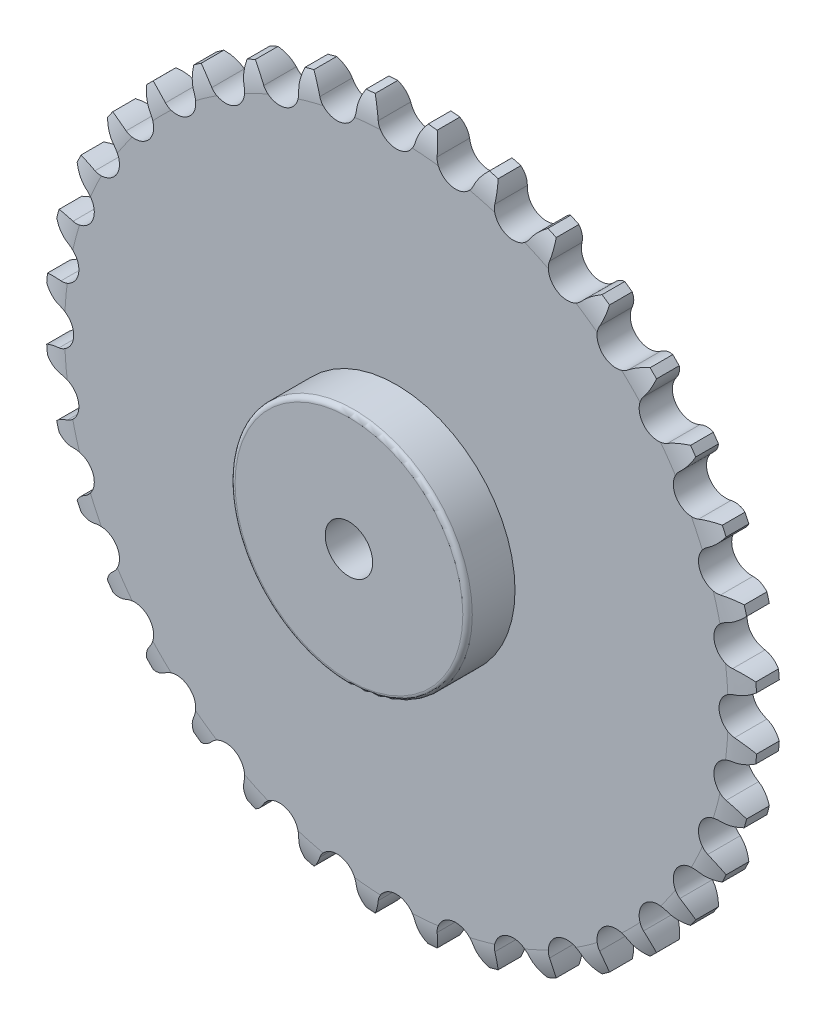
SolidWorks part; units mm, degrees
ref_plane "Front Plane" through (0, 0, 0) normal (0, 0, 1) x (1, 0, 0)
ref_plane "Top Plane" through (0, 0, 0) normal (0, 1, 0) x (1, 0, 0)
ref_plane "Right Plane" through (0, 0, 0) normal (1, 0, 0) x (0, 0, -1)
sketch "Sketch1" plane through (0, 0, 0) normal (0, 0, 1) x (1, 0, 0)
  line L0 (0, 0) -> (0, 75) construction
  line L1 (0, 0) -> (13.6677, 73.7441) construction
  circle A0 centre (0, 0) radius 15
  arc A1 (32.5641, 67.5617) -> (30.8234, 68.3734) centre (0, 0) ccw
  circle A2 centre (0, 0) radius 70.5 construction
  circle A3 centre (0, 0) radius 72 construction
  arc A4 (-3.9118, 71.1646) -> (3.9118, 71.1646) centre (0, 72) ccw
  arc A6 (5.5795, 74.7922) -> (3.9118, 71.1646) centre (12.8364, 69.2588) ccw
  arc A7 (-5.5795, 74.7922) -> (-3.9118, 71.1646) centre (-12.8364, 69.2588) cw
  arc A8 (7.4928, 74.6248) -> (8.5052, 70.7628) centre (-0.6147, 70.4356) cw
  arc A9 (18.4823, 72.687) -> (16.21, 69.4042) centre (24.668, 65.9776) ccw
  arc A10 (8.5052, 70.7628) -> (16.21, 69.4042) centre (12.5027, 70.9062) ccw
  arc A11 (20.3374, 72.19) -> (20.6639, 68.2108) centre (11.6257, 69.4723) cw
  arc A12 (30.8234, 68.3734) -> (28.0156, 65.535) centre (35.7502, 60.6917) ccw
  arc A13 (20.6639, 68.2108) -> (28.0156, 65.535) centre (24.6255, 67.6579) ccw
  arc A14 (32.5641, 67.5617) -> (32.1946, 63.5863) centre (23.5128, 66.3981) cw
  arc A15 (42.2281, 61.9822) -> (38.97, 59.6745) centre (45.746, 53.5617) ccw
  arc A16 (32.1946, 63.5863) -> (38.97, 59.6745) centre (36, 62.3538) ccw
  arc A17 (43.8013, 60.8806) -> (42.7471, 57.0297) centre (34.6855, 61.3064) cw
  arc A18 (52.3496, 53.7077) -> (48.7404, 52.0008) centre (54.3519, 44.8043) ccw
  arc A19 (42.7471, 57.0297) -> (48.7404, 52.0008) centre (46.2807, 55.1552) ccw
  arc A20 (53.7077, 52.3496) -> (52.0008, 48.7404) centre (44.8043, 54.3519) cw
  arc A21 (60.8806, 43.8013) -> (57.0297, 42.7471) centre (61.3064, 34.6855) ccw
  arc A22 (52.0008, 48.7404) -> (57.0297, 42.7471) centre (55.1552, 46.2807) ccw
  arc A23 (61.9822, 42.2281) -> (59.6745, 38.97) centre (53.5617, 45.746) cw
  arc A24 (67.5617, 32.5641) -> (63.5863, 32.1946) centre (66.3981, 23.5128) ccw
  arc A25 (59.6745, 38.97) -> (63.5863, 32.1946) centre (62.3538, 36) ccw
  arc A26 (68.3734, 30.8234) -> (65.535, 28.0156) centre (60.6917, 35.7502) cw
  arc A27 (72.19, 20.3374) -> (68.2108, 20.6639) centre (69.4723, 11.6257) ccw
  arc A28 (65.535, 28.0156) -> (68.2108, 20.6639) centre (67.6579, 24.6255) ccw
  arc A29 (72.687, 18.4823) -> (69.4042, 16.21) centre (65.9776, 24.668) cw
  arc A30 (74.6248, 7.4928) -> (70.7628, 8.5052) centre (70.4356, -0.6147) ccw
  arc A31 (69.4042, 16.21) -> (70.7628, 8.5052) centre (70.9062, 12.5027) ccw
  arc A32 (74.7922, 5.5795) -> (71.1646, 3.9118) centre (69.2588, 12.8364) cw
  arc A33 (74.7922, -5.5795) -> (71.1646, -3.9118) centre (69.2588, -12.8364) ccw
  arc A34 (71.1646, 3.9118) -> (71.1646, -3.9118) centre (72, 0) ccw
  arc A35 (74.6248, -7.4928) -> (70.7628, -8.5052) centre (70.4356, 0.6147) cw
  arc A36 (72.687, -18.4823) -> (69.4042, -16.21) centre (65.9776, -24.668) ccw
  arc A37 (70.7628, -8.5052) -> (69.4042, -16.21) centre (70.9062, -12.5027) ccw
  arc A38 (72.19, -20.3374) -> (68.2108, -20.6639) centre (69.4723, -11.6257) cw
  arc A39 (68.3734, -30.8234) -> (65.535, -28.0156) centre (60.6917, -35.7502) ccw
  arc A40 (68.2108, -20.6639) -> (65.535, -28.0156) centre (67.6579, -24.6255) ccw
  arc A41 (67.5617, -32.5641) -> (63.5863, -32.1946) centre (66.3981, -23.5128) cw
  arc A42 (61.9822, -42.2281) -> (59.6745, -38.97) centre (53.5617, -45.746) ccw
  arc A43 (63.5863, -32.1946) -> (59.6745, -38.97) centre (62.3538, -36) ccw
  arc A44 (60.8806, -43.8013) -> (57.0297, -42.7471) centre (61.3064, -34.6855) cw
  arc A45 (53.7077, -52.3496) -> (52.0008, -48.7404) centre (44.8043, -54.3519) ccw
  arc A46 (57.0297, -42.7471) -> (52.0008, -48.7404) centre (55.1552, -46.2807) ccw
  arc A47 (52.3496, -53.7077) -> (48.7404, -52.0008) centre (54.3519, -44.8043) cw
  arc A48 (43.8013, -60.8806) -> (42.7471, -57.0297) centre (34.6855, -61.3064) ccw
  arc A49 (48.7404, -52.0008) -> (42.7471, -57.0297) centre (46.2807, -55.1552) ccw
  arc A50 (42.2281, -61.9822) -> (38.97, -59.6745) centre (45.746, -53.5617) cw
  arc A51 (32.5641, -67.5617) -> (32.1946, -63.5863) centre (23.5128, -66.3981) ccw
  arc A52 (38.97, -59.6745) -> (32.1946, -63.5863) centre (36, -62.3538) ccw
  arc A53 (30.8234, -68.3734) -> (28.0156, -65.535) centre (35.7502, -60.6917) cw
  arc A54 (20.3374, -72.19) -> (20.6639, -68.2108) centre (11.6257, -69.4723) ccw
  arc A55 (28.0156, -65.535) -> (20.6639, -68.2108) centre (24.6255, -67.6579) ccw
  arc A56 (18.4823, -72.687) -> (16.21, -69.4042) centre (24.668, -65.9776) cw
  arc A57 (7.4928, -74.6248) -> (8.5052, -70.7628) centre (-0.6147, -70.4356) ccw
  arc A58 (16.21, -69.4042) -> (8.5052, -70.7628) centre (12.5027, -70.9062) ccw
  arc A59 (5.5795, -74.7922) -> (3.9118, -71.1646) centre (12.8364, -69.2588) cw
  arc A60 (-5.5795, -74.7922) -> (-3.9118, -71.1646) centre (-12.8364, -69.2588) ccw
  arc A61 (3.9118, -71.1646) -> (-3.9118, -71.1646) centre (0, -72) ccw
  arc A62 (-7.4928, -74.6248) -> (-8.5052, -70.7628) centre (0.6147, -70.4356) cw
  arc A63 (-18.4823, -72.687) -> (-16.21, -69.4042) centre (-24.668, -65.9776) ccw
  arc A64 (-8.5052, -70.7628) -> (-16.21, -69.4042) centre (-12.5027, -70.9062) ccw
  arc A65 (-20.3374, -72.19) -> (-20.6639, -68.2108) centre (-11.6257, -69.4723) cw
  arc A66 (-30.8234, -68.3734) -> (-28.0156, -65.535) centre (-35.7502, -60.6917) ccw
  arc A67 (-20.6639, -68.2108) -> (-28.0156, -65.535) centre (-24.6255, -67.6579) ccw
  arc A68 (-32.5641, -67.5617) -> (-32.1946, -63.5863) centre (-23.5128, -66.3981) cw
  arc A69 (-42.2281, -61.9822) -> (-38.97, -59.6745) centre (-45.746, -53.5617) ccw
  arc A70 (-32.1946, -63.5863) -> (-38.97, -59.6745) centre (-36, -62.3538) ccw
  arc A71 (-43.8013, -60.8806) -> (-42.7471, -57.0297) centre (-34.6855, -61.3064) cw
  arc A72 (-52.3496, -53.7077) -> (-48.7404, -52.0008) centre (-54.3519, -44.8043) ccw
  arc A73 (-42.7471, -57.0297) -> (-48.7404, -52.0008) centre (-46.2807, -55.1552) ccw
  arc A74 (-53.7077, -52.3496) -> (-52.0008, -48.7404) centre (-44.8043, -54.3519) cw
  arc A75 (-60.8806, -43.8013) -> (-57.0297, -42.7471) centre (-61.3064, -34.6855) ccw
  arc A76 (-52.0008, -48.7404) -> (-57.0297, -42.7471) centre (-55.1552, -46.2807) ccw
  arc A77 (-61.9822, -42.2281) -> (-59.6745, -38.97) centre (-53.5617, -45.746) cw
  arc A78 (-67.5617, -32.5641) -> (-63.5863, -32.1946) centre (-66.3981, -23.5128) ccw
  arc A79 (-59.6745, -38.97) -> (-63.5863, -32.1946) centre (-62.3538, -36) ccw
  arc A80 (-68.3734, -30.8234) -> (-65.535, -28.0156) centre (-60.6917, -35.7502) cw
  arc A81 (-72.19, -20.3374) -> (-68.2108, -20.6639) centre (-69.4723, -11.6257) ccw
  arc A82 (-65.535, -28.0156) -> (-68.2108, -20.6639) centre (-67.6579, -24.6255) ccw
  arc A83 (-72.687, -18.4823) -> (-69.4042, -16.21) centre (-65.9776, -24.668) cw
  arc A84 (-74.6248, -7.4928) -> (-70.7628, -8.5052) centre (-70.4356, 0.6147) ccw
  arc A85 (-69.4042, -16.21) -> (-70.7628, -8.5052) centre (-70.9062, -12.5027) ccw
  arc A86 (-74.7922, -5.5795) -> (-71.1646, -3.9118) centre (-69.2588, -12.8364) cw
  arc A87 (-74.7922, 5.5795) -> (-71.1646, 3.9118) centre (-69.2588, 12.8364) ccw
  arc A88 (-71.1646, -3.9118) -> (-71.1646, 3.9118) centre (-72, 0) ccw
  arc A89 (-74.6248, 7.4928) -> (-70.7628, 8.5052) centre (-70.4356, -0.6147) cw
  arc A90 (-72.687, 18.4823) -> (-69.4042, 16.21) centre (-65.9776, 24.668) ccw
  arc A91 (-70.7628, 8.5052) -> (-69.4042, 16.21) centre (-70.9062, 12.5027) ccw
  arc A92 (-72.19, 20.3374) -> (-68.2108, 20.6639) centre (-69.4723, 11.6257) cw
  arc A93 (-68.3734, 30.8234) -> (-65.535, 28.0156) centre (-60.6917, 35.7502) ccw
  arc A94 (-68.2108, 20.6639) -> (-65.535, 28.0156) centre (-67.6579, 24.6255) ccw
  arc A95 (-67.5617, 32.5641) -> (-63.5863, 32.1946) centre (-66.3981, 23.5128) cw
  arc A96 (-61.9822, 42.2281) -> (-59.6745, 38.97) centre (-53.5617, 45.746) ccw
  arc A97 (-63.5863, 32.1946) -> (-59.6745, 38.97) centre (-62.3538, 36) ccw
  arc A98 (-60.8806, 43.8013) -> (-57.0297, 42.7471) centre (-61.3064, 34.6855) cw
  arc A99 (-53.7077, 52.3496) -> (-52.0008, 48.7404) centre (-44.8043, 54.3519) ccw
  arc A100 (-57.0297, 42.7471) -> (-52.0008, 48.7404) centre (-55.1552, 46.2807) ccw
  arc A101 (-52.3496, 53.7077) -> (-48.7404, 52.0008) centre (-54.3519, 44.8043) cw
  arc A102 (-43.8013, 60.8806) -> (-42.7471, 57.0297) centre (-34.6855, 61.3064) ccw
  arc A103 (-48.7404, 52.0008) -> (-42.7471, 57.0297) centre (-46.2807, 55.1552) ccw
  arc A104 (-42.2281, 61.9822) -> (-38.97, 59.6745) centre (-45.746, 53.5617) cw
  arc A105 (-32.5641, 67.5617) -> (-32.1946, 63.5863) centre (-23.5128, 66.3981) ccw
  arc A106 (-38.97, 59.6745) -> (-32.1946, 63.5863) centre (-36, 62.3538) ccw
  arc A107 (-30.8234, 68.3734) -> (-28.0156, 65.535) centre (-35.7502, 60.6917) cw
  arc A108 (-20.3374, 72.19) -> (-20.6639, 68.2108) centre (-11.6257, 69.4723) ccw
  arc A109 (-28.0156, 65.535) -> (-20.6639, 68.2108) centre (-24.6255, 67.6579) ccw
  arc A110 (-18.4823, 72.687) -> (-16.21, 69.4042) centre (-24.668, 65.9776) cw
  arc A111 (-7.4928, 74.6248) -> (-8.5052, 70.7628) centre (0.6147, 70.4356) ccw
  arc A112 (-16.21, 69.4042) -> (-8.5052, 70.7628) centre (-12.5027, 70.9062) ccw
  arc A113 (43.8013, 60.8806) -> (42.2281, 61.9822) centre (0, 0) ccw
  arc A114 (53.7077, 52.3496) -> (52.3496, 53.7077) centre (0, 0) ccw
  arc A115 (61.9822, 42.2281) -> (60.8806, 43.8013) centre (0, 0) ccw
  arc A116 (68.3734, 30.8234) -> (67.5617, 32.5641) centre (0, 0) ccw
  arc A117 (72.687, 18.4823) -> (72.19, 20.3374) centre (0, 0) ccw
  arc A118 (74.7922, 5.5795) -> (74.6248, 7.4928) centre (0, 0) ccw
  arc A119 (74.6248, -7.4928) -> (74.7922, -5.5795) centre (0, 0) ccw
  arc A120 (72.19, -20.3374) -> (72.687, -18.4823) centre (0, 0) ccw
  arc A121 (60.8806, -43.8013) -> (61.9822, -42.2281) centre (0, 0) ccw
  arc A122 (67.5617, -32.5641) -> (68.3734, -30.8234) centre (0, 0) ccw
  arc A123 (52.3496, -53.7077) -> (53.7077, -52.3496) centre (0, 0) ccw
  arc A124 (42.2281, -61.9822) -> (43.8013, -60.8806) centre (0, 0) ccw
  arc A125 (30.8234, -68.3734) -> (32.5641, -67.5617) centre (0, 0) ccw
  arc A126 (18.4823, -72.687) -> (20.3374, -72.19) centre (0, 0) ccw
  arc A127 (5.5795, -74.7922) -> (7.4928, -74.6248) centre (0, 0) ccw
  arc A128 (-7.4928, -74.6248) -> (-5.5795, -74.7922) centre (0, 0) ccw
  arc A129 (-20.3374, -72.19) -> (-18.4823, -72.687) centre (0, 0) ccw
  arc A130 (-32.5641, -67.5617) -> (-30.8234, -68.3734) centre (0, 0) ccw
  arc A131 (-43.8013, -60.8806) -> (-42.2281, -61.9822) centre (0, 0) ccw
  arc A132 (-53.7077, -52.3496) -> (-52.3496, -53.7077) centre (0, 0) ccw
  arc A133 (-61.9822, -42.2281) -> (-60.8806, -43.8013) centre (0, 0) ccw
  arc A134 (-68.3734, -30.8234) -> (-67.5617, -32.5641) centre (0, 0) ccw
  arc A135 (-72.687, -18.4823) -> (-72.19, -20.3374) centre (0, 0) ccw
  arc A136 (-74.7922, -5.5795) -> (-74.6248, -7.4928) centre (0, 0) ccw
  arc A137 (-74.6248, 7.4928) -> (-74.7922, 5.5795) centre (0, 0) ccw
  arc A138 (-72.19, 20.3374) -> (-72.687, 18.4823) centre (0, 0) ccw
  arc A139 (-67.5617, 32.5641) -> (-68.3734, 30.8234) centre (0, 0) ccw
  arc A140 (-60.8806, 43.8013) -> (-61.9822, 42.2281) centre (0, 0) ccw
  arc A141 (-52.3496, 53.7077) -> (-53.7077, 52.3496) centre (0, 0) ccw
  arc A142 (-42.2281, 61.9822) -> (-43.8013, 60.8806) centre (0, 0) ccw
  arc A143 (-30.8234, 68.3734) -> (-32.5641, 67.5617) centre (0, 0) ccw
  arc A144 (-18.4823, 72.687) -> (-20.3374, 72.19) centre (0, 0) ccw
  arc A145 (-5.5795, 74.7922) -> (-7.4928, 74.6248) centre (0, 0) ccw
  arc A146 (7.4928, 74.6248) -> (5.5795, 74.7922) centre (0, 0) ccw
  arc A147 (20.3374, 72.19) -> (18.4823, 72.687) centre (0, 0) ccw
  point P263 (0, 0)
  dimension "D1" = 150
  dimension "D2" = 144
  dimension "D3" = 141
  dimension "D4" = 30
  dimension "D6" = 8
  dimension "D7" = 36
  dimension "D5" = 10.5
extrude "Boss-Extrude1" add sketch "Sketch1" along normal mid plane 7
sketch "Sketch2" plane through (0, 0, 0) normal (1, 0, 0) x (0, 0, -1)
  line L0 (4.5, 69.7922) -> (3.5, 69.7922)
  line L1 (4.5, 75.7922) -> (4.5, 69.7922)
  line L2 (-3.5, 75.7922) -> (3.5, 75.7922)
  line L3 (-4.5, 75.7922) -> (-2, 75.7922)
  line L4 (-4.5, 69.7922) -> (-3.5, 69.7922)
  line L5 (-4.5, 74.6248) -> (-4.5, 70.7628)
  line L6 (-4.5, 75.7922) -> (-4.5, 69.7922)
  line L7 (-3.5, 75.7922) -> (3.5, 75.7922) construction
  line L8 (-3.5, 69.7922) -> (3.5, 69.7922) construction
  line L9 (-3.5, 72.19) -> (-3.5, 68.2108) construction
  line L10 (0, 75.7922) -> (0, 67.5617) construction
  line L11 (-3.5, 67.5617) -> (3.5, 67.5617) construction
  line L12 (4.5, 75.7922) -> (2, 75.7922)
  arc A0 (-3.5, 69.7922) -> (-2, 75.7922) centre (8.9998, 69.8547) cw
  arc A1 (3.5, 69.7922) -> (2, 75.7922) centre (-8.9998, 69.8547) ccw
  dimension "D4" = 12.5
  dimension "D5" = 1.5
  dimension "D1" = 1
  dimension "D2" = 1
  dimension "D3" = 6
revolve "Cut-Revolve2" cut sketch "Sketch2" angle 360 about axis through (0, 0, 3.5) along (0, 0, -1)
sketch "Sketch3" plane through (0, 0, 3.5) normal (0, 0, 1) x (1, 0, 0)
  circle A0 centre (0, 0) radius 15
  circle A1 centre (0, 0) radius 5
  dimension "D1" = 10
extrude "Boss-Extrude2" add sketch "Sketch3" against normal blind 7
sketch "Sketch4" plane through (0, 0, 3.5) normal (0, 0, 1) x (1, 0, 0)
  circle A0 centre (0, 0) radius 5
  circle A1 centre (0, 0) radius 25
  dimension "D1" = 50
extrude "Boss-Extrude3" add sketch "Sketch4" along normal blind 10
fillet "Fillet1" radius 1 1 edges at (25, 0, 13.5)
